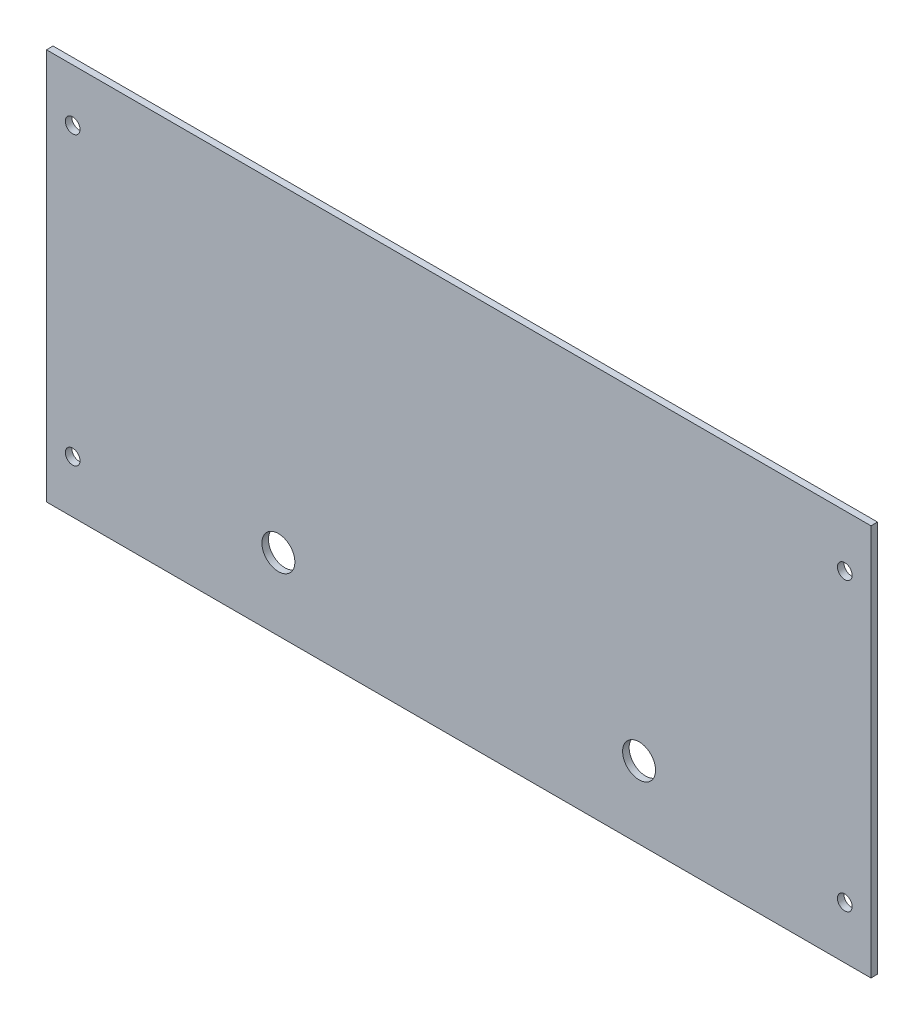
SolidWorks part; units mm, degrees
ref_plane "Front Plane" through (0, 0, 0) normal (0, 0, 1) x (1, 0, 0)
ref_plane "Top Plane" through (0, 0, 0) normal (0, 1, 0) x (1, 0, 0)
ref_plane "Right Plane" through (0, 0, 0) normal (1, 0, 0) x (0, 0, -1)
sketch "Sketch1" plane through (0, 0, 0) normal (0, 0, 1) x (1, 0, 0)
  line L0 (-87.5, -60) -> (87.5, -60) construction
  line L1 (-200, -95) -> (200, -95)
  line L2 (-200, -95) -> (-200, 95)
  line L3 (-200, 95) -> (200, 95)
  line L4 (200, -95) -> (200, 95)
  line L5 (-200, -95) -> (200, 95) construction
  line L6 (-200, 95) -> (200, -95) construction
  line L7 (0, 95) -> (0, -95) construction
  circle A0 centre (-87.5, -60) radius 8
  circle A1 centre (87.5, -60) radius 8
  circle A2 centre (-187.3, 69.6) radius 3.5687
  circle A3 centre (-187.3, -69.6) radius 3.5687
  circle A4 centre (187.3, -69.6) radius 3.5687
  circle A5 centre (187.3, 69.6) radius 3.5687
  point P0 (0, 0)
  point P9 (0, -60)
  dimension "D4" = 16
  dimension "D9" = 7.1374
  dimension "D1" = 190
  dimension "D2" = 400
  dimension "D3" = 35
  dimension "D5" = 175
  dimension "D6" = 12.7
  dimension "D7" = 25.4
  dimension "D8" = 25.4
extrude "Boss-Extrude1" add sketch "Sketch1" along normal blind 3.175
